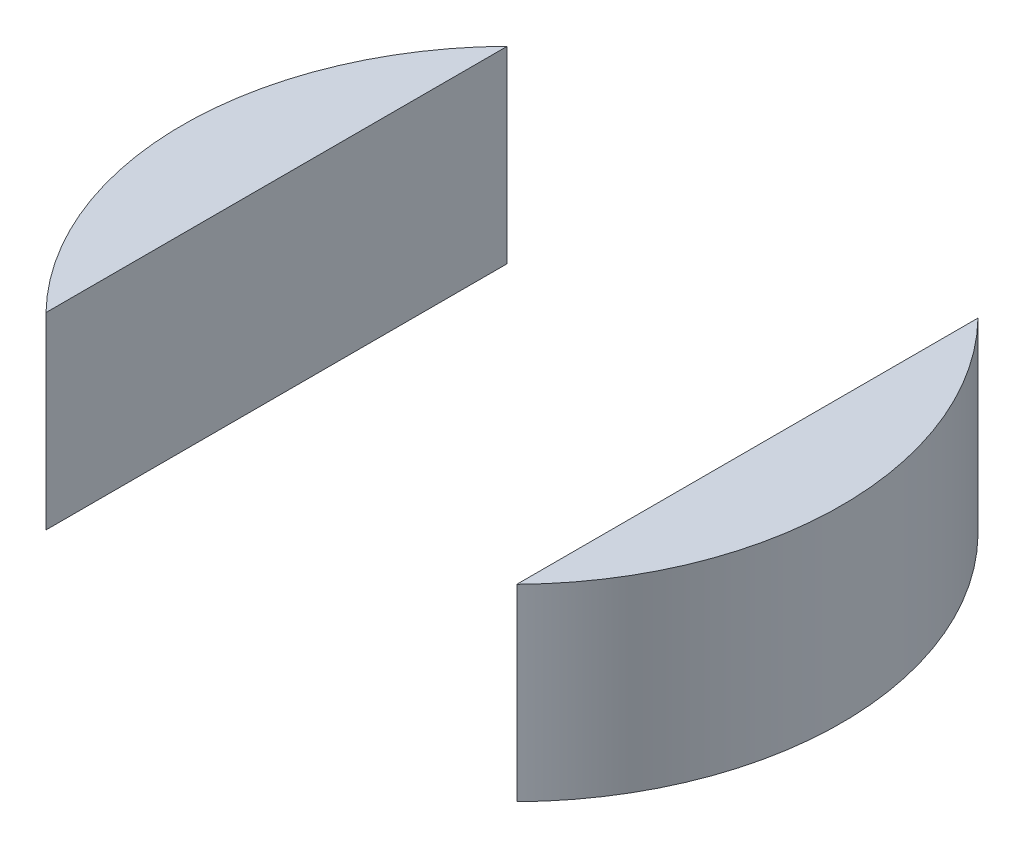
SolidWorks part; units mm, degrees
ref_plane "Front Plane" through (0, 0, 0) normal (0, 0, 1) x (1, 0, 0)
ref_plane "Top Plane" through (0, 0, 0) normal (0, 1, 0) x (1, 0, 0)
ref_plane "Right Plane" through (0, 0, 0) normal (1, 0, 0) x (0, 0, -1)
sketch "Sketch2" plane through (0, 0, 0) normal (0, 1, 0) x (1, 0, 0)
  line L0 (0, 0) -> (-12.5, 0) construction
  line L1 (-12.5, 12.2474) -> (-12.5, -12.2474)
  line L2 (0, 0) -> (0, 17.5) construction
  line L3 (12.5, 12.2474) -> (12.5, -12.2474)
  line L4 (-16, 0) -> (16, 0) construction
  line L5 (-8.2864, 0) -> (-8.2864, 1)
  line L6 (-15.9687, 1) -> (15.9687, 1)
  line L7 (-15.9687, -1) -> (15.9687, -1)
  circle A0 centre (0, 0) radius 17.5
  circle A1 centre (0, 0) radius 16
  circle A2 centre (0, 0) radius 6.25
  dimension "D1" = 35
  dimension "D3" = 32
  dimension "D4" = 12.5
  dimension "D2" = 12.5
  dimension "D5" = 1
extrude "Boss-Extrude1" add sketch "Sketch2" along normal blind 10 contours A1 L1 A0 | L1 A1 L6 | L7 A1 L1 | L6 A1 L7 L1 | A1 L3 A0 | L6 A1 L3 | L7 A1 L6 L3 | L3 A1 L7
